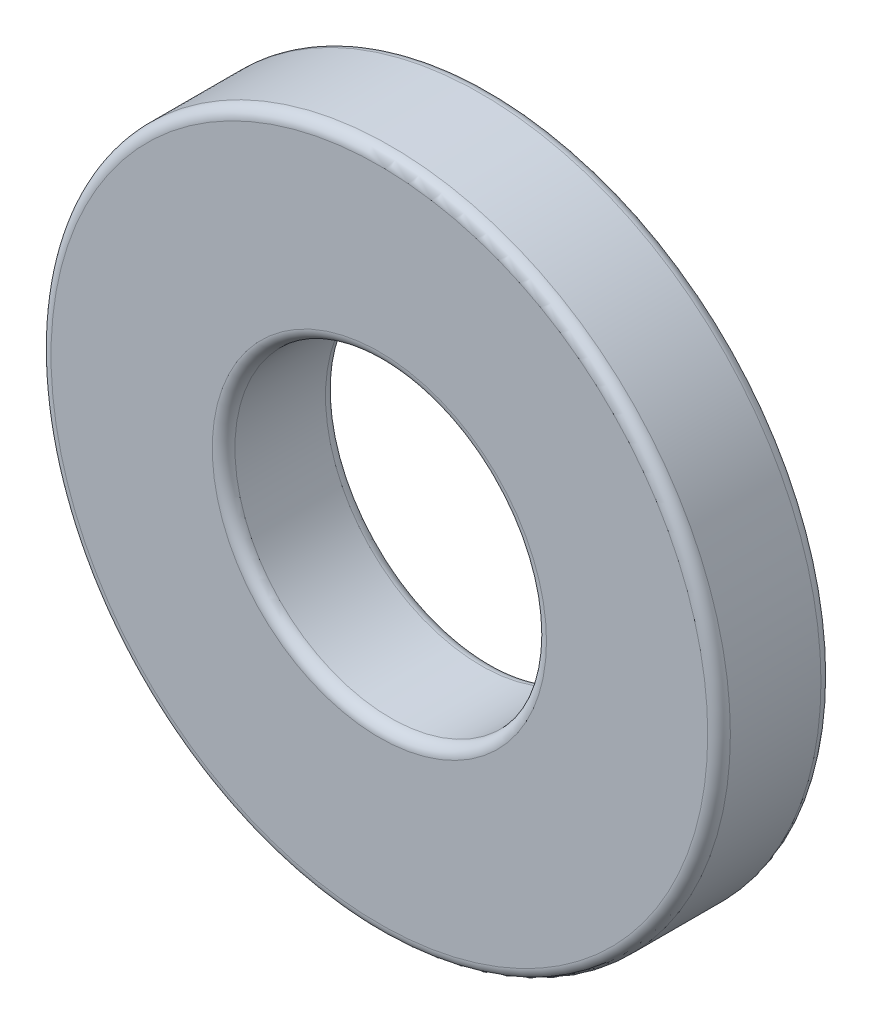
SolidWorks part; units mm, degrees
ref_plane "Front Plane" through (0, 0, 0) normal (0, 0, 1) x (1, 0, 0)
ref_plane "Top Plane" through (0, 0, 0) normal (0, 1, 0) x (1, 0, 0)
ref_plane "Right Plane" through (0, 0, 0) normal (1, 0, 0) x (0, 0, -1)
sketch "Sketch1" plane through (0, 0, 0) normal (0, 0, 1) x (1, 0, 0)
  circle A0 centre (0, 0) radius 4.3688
  circle A1 centre (0, 0) radius 9.525
  point P4 (0, 9.525)
  point P5 (0, 4.3688)
  point P6 (0, -4.3688)
  point P7 (4.3688, 0)
  point P8 (-4.3688, 0)
  dimension "OD" = 19.05
  dimension "ID" = 8.7376
sketch "Sketch2" plane through (0, 0, 0) normal (1, 0, 0) x (0, 0, -1)
  line L1 (-1.5875, 9.525) -> (1.5875, 9.525)
  line L2 (-1.5875, 9.525) -> (-1.5875, -9.525)
  line L3 (-1.5875, -9.525) -> (1.5875, -9.525)
  line L4 (1.5875, 9.525) -> (1.5875, -9.525)
  point P4 (0, 9.525)
  point P5 (1.5875, 0)
  dimension "Thickness" = 3.175
sketch "Sketch3" plane through (0, 0, 0) normal (0, 0, 1) x (1, 0, 0)
  circle A0 centre (0, 0) radius 4.3688 construction
  circle A1 centre (0, 0) radius 9.525 construction
  circle A2 centre (0, 0) radius 4.3688
  circle A3 centre (0, 0) radius 9.525
extrude "Boss-Extrude1" add sketch "Sketch3" against normal up to vertex (1.5875 mm away) from vertex at 1.5875 starting at point (0, 9.525, 1.5875)
fillet "Fillet1" radius 0.3175 4 edges at (4.3688, 0, 1.5875) (4.3688, 0, -1.5875) (9.525, 0, 1.5875) (9.525, 0, -1.5875)
equation "\"D1@Fillet1\"=\"Thickness@Sketch2\"*.1"
